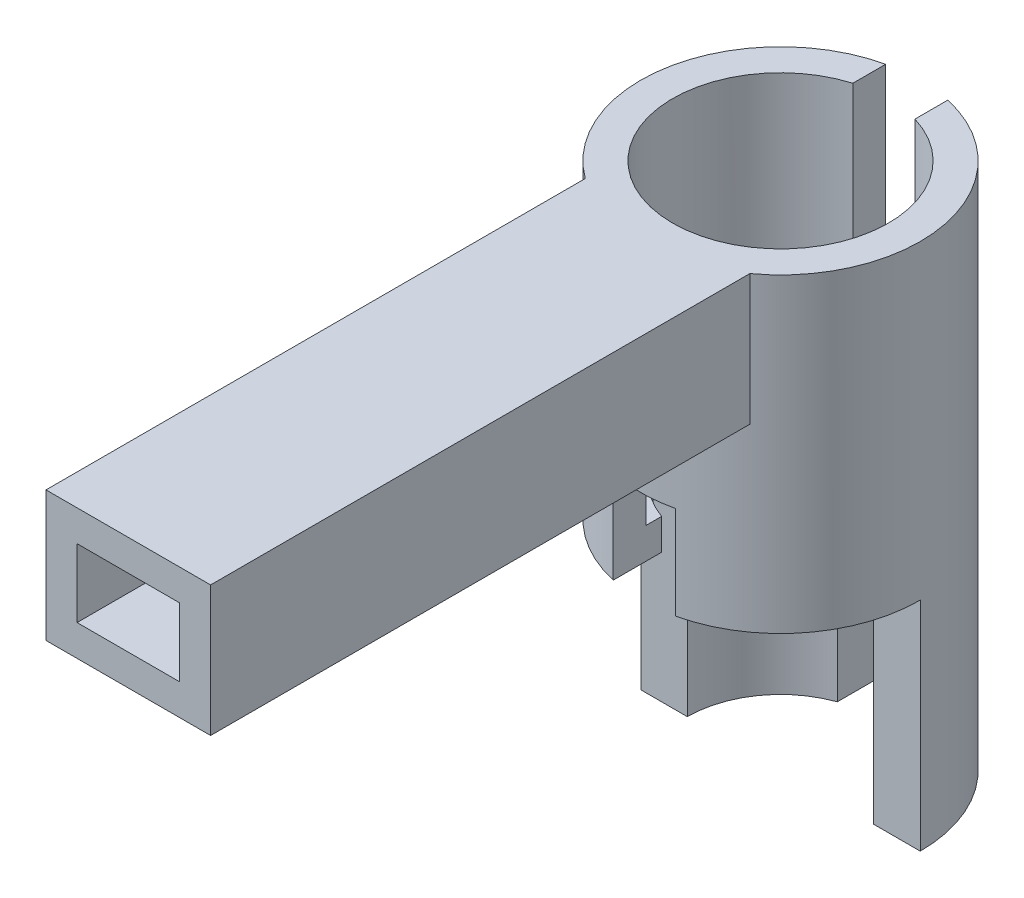
SolidWorks part; units mm, degrees
ref_plane "Front Plane" through (0, 0, 0) normal (0, 0, 1) x (1, 0, 0)
ref_plane "Top Plane" through (0, 0, 0) normal (0, 1, 0) x (1, 0, 0)
ref_plane "Right Plane" through (0, 0, 0) normal (1, 0, 0) x (0, 0, -1)
sketch "Sketch5" plane through (0, 0, 0) normal (0, 1, 0) x (1, 0, 0)
  circle A0 centre (0, 0) radius 4.5
  dimension "D1" = 9
extrude "Boss-Extrude2" add sketch "Sketch5" along normal blind 17
sketch "Sketch6" plane through (0, 17, 0) normal (0, 1, 0) x (1, 0, 0)
  circle A0 centre (0, 0) radius 3.475
  dimension "D1" = 6.95
extrude "Cut-Extrude2" cut sketch "Sketch6" against normal blind 9
sketch "Sketch7" plane through (0, 8, 0) normal (0, 1, 0) x (1, 0, 0)
  circle A0 centre (0, 0) radius 3
  dimension "D1" = 6
extrude "Cut-Extrude3" cut sketch "Sketch7" against normal through all
ref_plane "Plane1" through (0, 0, 3) normal (0, 0, 1) x (1, 0, 0)
sketch "Sketch8" plane through (0, 0, 3) normal (0, 0, 1) x (1, 0, 0)
  line L1 (-2.65, 12.8) -> (2.65, 12.8)
  line L2 (-2.65, 12.8) -> (-2.65, 17)
  line L3 (-2.65, 17) -> (2.65, 17)
  line L4 (2.65, 12.8) -> (2.65, 17)
  line L5 (-2.65, 12.8) -> (2.65, 17) construction
  line L6 (-2.65, 17) -> (2.65, 12.8) construction
  line L7 (0, 17) -> (0, 0) construction
  line L9 (4.5, 17) -> (-4.5, 17) construction
  point P0 (0, 14.9)
  point P5 (0, 17)
  dimension "D1" = 5.3
  dimension "D2" = 4.2
extrude "Boss-Extrude3" add sketch "Sketch8" along normal blind 18
sketch "Sketch9" plane through (0, 0, 21) normal (0, 0, 1) x (1, 0, 0)
  line L0 (0, 0) -> (0, 17) construction
  line L1 (-1.65, 13.8) -> (1.65, 13.8)
  line L2 (-1.65, 13.8) -> (-1.65, 16)
  line L3 (-1.65, 16) -> (1.65, 16)
  line L4 (1.65, 13.8) -> (1.65, 16)
  line L5 (-1.65, 13.8) -> (1.65, 16) construction
  line L6 (-1.65, 16) -> (1.65, 13.8) construction
  line L7 (2.65, 17) -> (-2.65, 17) construction
  line L8 (-2.65, 14.9) -> (2.65, 14.9) construction
  line L9 (-2.65, 17) -> (-2.65, 12.8) construction
  line L10 (2.65, 12.8) -> (2.65, 17) construction
  point P0 (0, 14.9)
  point P10 (0, 16)
  point P17 (-1.65, 14.9)
  dimension "D1" = 3.3
  dimension "D2" = 2.2
extrude "Cut-Extrude7" cut sketch "Sketch9" against normal blind 20
sketch "Sketch22" plane through (0, 0, 0) normal (0, 1, 0) x (1, 0, 0)
  line L1 (-1, -2.3902) -> (1, -2.3902)
  line L2 (-1, -2.3902) -> (-1, -6.6098)
  line L3 (-1, -6.6098) -> (1, -6.6098)
  line L4 (1, -2.3902) -> (1, -6.6098)
  line L5 (-1, -2.3902) -> (1, -6.6098) construction
  line L6 (-1, -6.6098) -> (1, -2.3902) construction
  circle A0 centre (0, 0) radius 4.5 construction
  point P0 (0, -4.5)
  dimension "D1" = 2
extrude "Cut-Extrude17" cut sketch "Sketch22" along normal blind 10
sketch "Sketch23" plane through (0, 0, 0) normal (0, 1, 0) x (1, 0, 0)
  line L1 (7.4234, 0) -> (-7.8996, 0)
  line L2 (7.4234, 0) -> (7.4234, -5.2083)
  line L3 (7.4234, -5.2083) -> (-7.8996, -5.2083)
  line L4 (-7.8996, 0) -> (-7.8996, -5.2083)
extrude "Cut-Extrude18" cut sketch "Sketch23" along normal blind 7
sketch "Sketch24" plane through (0, 0, 0) normal (0, 1, 0) x (1, 0, 0)
  line L1 (1, 1.7865) -> (-1, 1.7865)
  line L2 (1, 1.7865) -> (1, 7.2135)
  line L3 (1, 7.2135) -> (-1, 7.2135)
  line L4 (-1, 1.7865) -> (-1, 7.2135)
  line L5 (1, 1.7865) -> (-1, 7.2135) construction
  line L6 (1, 7.2135) -> (-1, 1.7865) construction
  arc A0 (4.5, 0) -> (-4.5, 0) centre (0, 0) ccw construction
  point P0 (0, 4.5)
  dimension "D1" = 2
extrude "Cut-Extrude19" cut sketch "Sketch24" along normal through all both and the other way through all
sketch "Sketch26" plane through (0, 17, 0) normal (0, 1, 0) x (1, 0, 0)
  circle A0 centre (0, 0) radius 3.475
extrude "Cut-Extrude21" cut sketch "Sketch26" against normal blind 7
